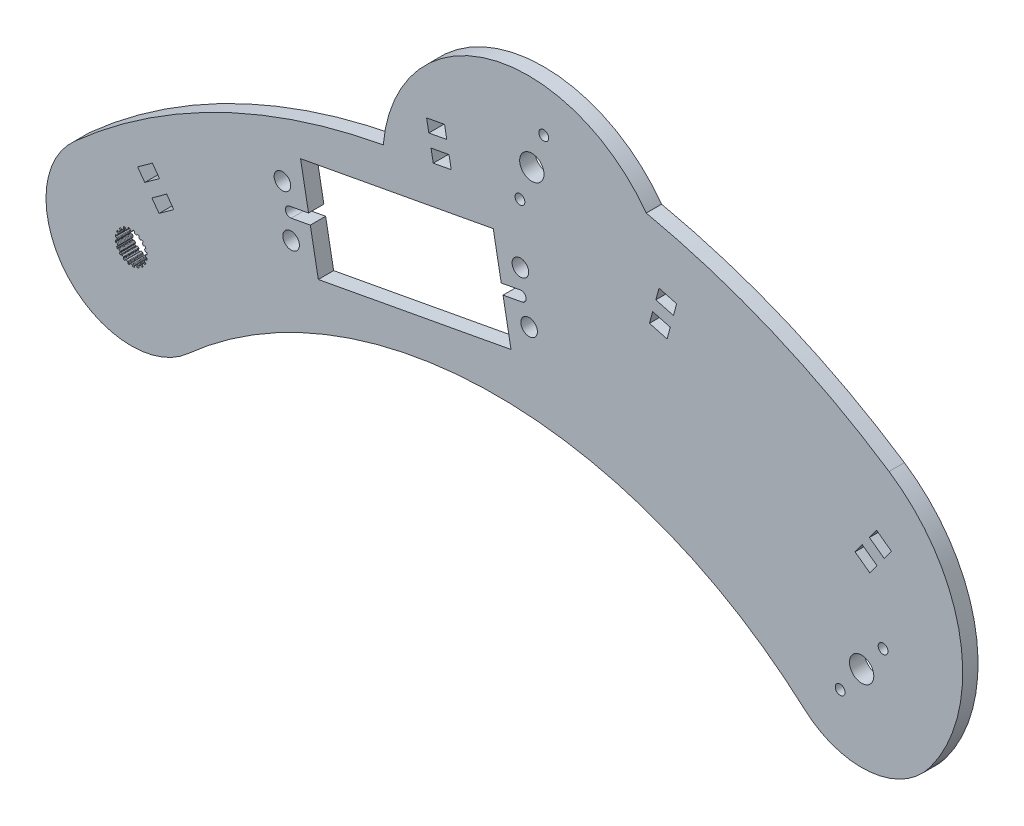
SolidWorks part; units mm, degrees
ref_plane "Front Plane" through (0, 0, 0) normal (0, 0, 1) x (1, 0, 0)
ref_plane "Top Plane" through (0, 0, 0) normal (0, 1, 0) x (1, 0, 0)
ref_plane "Right Plane" through (0, 0, 0) normal (1, 0, 0) x (0, 0, -1)
sketch "Sketch1" plane through (0, 0, 0) normal (0, 0, 1) x (1, 0, 0)
  line L0 (-0.1069, 2.9699) -> (0.1069, 2.9699)
  line L1 (0.3159, 3.2375) -> (0.2537, 3.0575)
  line L2 (-0.2964, 3.2367) -> (-0.2318, 3.0575)
  line L3 (-0.2964, 3.2367) -> (0.3159, 3.2375) construction
  line L4 (0, 3.3252) -> (0, 0) construction
  line L5 (-0.2318, 3.0575) -> (0.2537, 3.0575) construction
  line L6 (-0.4281, 3.3241) -> (0.4281, 3.3263) construction
  line L7 (0.7183, 3.1698) -> (0.7244, 2.9795)
  line L8 (0.816, 2.8576) -> (1.0195, 2.7915)
  line L9 (1.3009, 2.9815) -> (1.1862, 2.8295)
  line L10 (1.6627, 2.7927) -> (1.6097, 2.6099)
  line L11 (1.6591, 2.4655) -> (1.8322, 2.3398)
  line L12 (2.1585, 2.4335) -> (2.0025, 2.3245)
  line L13 (2.4443, 2.1423) -> (2.3374, 1.9847)
  line L14 (2.3398, 1.8322) -> (2.4655, 1.6591)
  line L15 (2.8049, 1.6474) -> (2.6228, 1.5919)
  line L16 (2.9866, 1.2821) -> (2.8363, 1.1653)
  line L17 (2.7915, 1.0195) -> (2.8576, 0.816)
  line L18 (3.1767, 0.7) -> (2.9863, 0.7035)
  line L19 (3.2367, 0.2964) -> (3.0575, 0.2318)
  line L20 (2.9699, 0.1069) -> (2.9699, -0.1069)
  line L21 (3.2375, -0.3159) -> (3.0575, -0.2537)
  line L22 (3.1698, -0.7183) -> (2.9795, -0.7244)
  line L23 (2.8576, -0.816) -> (2.7915, -1.0195)
  line L24 (2.9815, -1.3009) -> (2.8295, -1.1862)
  line L25 (2.7927, -1.6627) -> (2.6099, -1.6097)
  line L26 (2.4655, -1.6591) -> (2.3398, -1.8322)
  line L27 (2.4335, -2.1585) -> (2.3245, -2.0025)
  line L28 (2.1423, -2.4443) -> (1.9847, -2.3374)
  line L29 (1.8322, -2.3398) -> (1.6591, -2.4655)
  line L30 (1.6474, -2.8049) -> (1.5919, -2.6228)
  line L31 (1.2821, -2.9866) -> (1.1653, -2.8363)
  line L32 (1.0195, -2.7915) -> (0.816, -2.8576)
  line L33 (0.7, -3.1767) -> (0.7035, -2.9863)
  line L34 (0.2964, -3.2367) -> (0.2318, -3.0575)
  line L35 (0.1069, -2.9699) -> (-0.1069, -2.9699)
  line L36 (-0.3159, -3.2375) -> (-0.2537, -3.0575)
  line L37 (-0.7183, -3.1698) -> (-0.7244, -2.9795)
  line L38 (-0.816, -2.8576) -> (-1.0195, -2.7915)
  line L39 (-1.3009, -2.9815) -> (-1.1862, -2.8295)
  line L40 (-1.6627, -2.7927) -> (-1.6097, -2.6099)
  line L41 (-1.6591, -2.4655) -> (-1.8322, -2.3398)
  line L42 (-2.1585, -2.4335) -> (-2.0025, -2.3245)
  line L43 (-2.4443, -2.1423) -> (-2.3374, -1.9847)
  line L44 (-2.3398, -1.8322) -> (-2.4655, -1.6591)
  line L45 (-2.8049, -1.6474) -> (-2.6228, -1.5919)
  line L46 (-2.9866, -1.2821) -> (-2.8363, -1.1653)
  line L47 (-2.7915, -1.0195) -> (-2.8576, -0.816)
  line L48 (-3.1767, -0.7) -> (-2.9863, -0.7035)
  line L49 (-3.2367, -0.2964) -> (-3.0575, -0.2318)
  line L50 (-2.9699, -0.1069) -> (-2.9699, 0.1069)
  line L51 (-3.2375, 0.3159) -> (-3.0575, 0.2537)
  line L52 (-3.1698, 0.7183) -> (-2.9795, 0.7244)
  line L53 (-2.8576, 0.816) -> (-2.7915, 1.0195)
  line L54 (-2.9815, 1.3009) -> (-2.8295, 1.1862)
  line L55 (-2.7927, 1.6627) -> (-2.6099, 1.6097)
  line L56 (-2.4655, 1.6591) -> (-2.3398, 1.8322)
  line L57 (-2.4335, 2.1585) -> (-2.3245, 2.0025)
  line L58 (-2.1423, 2.4443) -> (-1.9847, 2.3374)
  line L59 (-1.8322, 2.3398) -> (-1.6591, 2.4655)
  line L60 (-1.6474, 2.8049) -> (-1.5919, 2.6228)
  line L61 (-1.2821, 2.9866) -> (-1.1653, 2.8363)
  line L62 (-1.0195, 2.7915) -> (-0.816, 2.8576)
  line L63 (-0.7, 3.1767) -> (-0.7035, 2.9863)
  line L64 (0.4281, 3.3263) -> (0.62, 3.2938)
  line L65 (1.4351, 3.0312) -> (1.6075, 2.9409)
  line L66 (2.3015, 2.4394) -> (2.4376, 2.3003)
  line L67 (2.9427, 1.6088) -> (3.0291, 1.4344)
  line L68 (3.2958, 0.6207) -> (3.3241, 0.4281)
  line L69 (3.3263, -0.4281) -> (3.2938, -0.62)
  line L70 (3.0312, -1.4351) -> (2.9409, -1.6075)
  line L71 (2.4394, -2.3015) -> (2.3003, -2.4376)
  line L72 (1.6088, -2.9427) -> (1.4344, -3.0291)
  line L73 (0.6207, -3.2958) -> (0.4281, -3.3241)
  line L74 (-0.4281, -3.3263) -> (-0.62, -3.2938)
  line L75 (-1.4351, -3.0312) -> (-1.6075, -2.9409)
  line L76 (-2.3015, -2.4394) -> (-2.4376, -2.3003)
  line L77 (-2.9427, -1.6088) -> (-3.0291, -1.4344)
  line L78 (-3.2958, -0.6207) -> (-3.3241, -0.4281)
  line L79 (-3.3263, 0.4281) -> (-3.2938, 0.62)
  line L80 (-3.0312, 1.4351) -> (-2.9409, 1.6075)
  line L81 (-2.4394, 2.3015) -> (-2.3003, 2.4376)
  line L82 (-1.6088, 2.9427) -> (-1.4344, 3.0291)
  line L83 (-0.6207, 3.2958) -> (-0.4281, 3.3241)
  line L84 (-11.8753, 13.2369) -> (11.8753, -13.2369) construction
  line L85 (164.2753, 13.2369) -> (140.5247, -13.2369) construction
  line L86 (0, 0) -> (152.4, 0) construction
  arc A0 (0.2537, 3.0575) -> (0.1069, 2.9699) centre (0.1283, 3.1009) cw
  arc A1 (-0.2318, 3.0575) -> (-0.1069, 2.9699) centre (-0.1069, 3.1026) ccw
  arc A2 (0.62, 3.2938) -> (0.7183, 3.1698) centre (0.5856, 3.1656) cw
  arc A3 (0.7244, 2.9795) -> (0.816, 2.8576) centre (0.857, 2.9838) ccw
  arc A4 (-0.4281, 3.3241) -> (-0.2964, 3.2367) centre (-0.4213, 3.1916) cw
  arc A5 (0.4281, 3.3263) -> (0.3159, 3.2375) centre (0.4413, 3.1942) ccw
  arc A6 (1.1862, 2.8295) -> (1.0195, 2.7915) centre (1.0802, 2.9095) cw
  arc A7 (1.4351, 3.0312) -> (1.3009, 2.9815) centre (1.4068, 2.9015) ccw
  arc A8 (1.6075, 2.9409) -> (1.6627, 2.7927) centre (1.5352, 2.8297) cw
  arc A9 (1.6097, 2.6099) -> (1.6591, 2.4655) centre (1.7371, 2.5729) ccw
  arc A10 (2.0025, 2.3245) -> (1.8322, 2.3398) centre (1.9264, 2.4332) cw
  arc A11 (2.3015, 2.4394) -> (2.1585, 2.4335) centre (2.2346, 2.3248) ccw
  arc A12 (2.4376, 2.3003) -> (2.4443, 2.1423) centre (2.3345, 2.2168) cw
  arc A13 (2.3374, 1.9847) -> (2.3398, 1.8322) centre (2.4472, 1.9102) ccw
  arc A14 (2.6228, 1.5919) -> (2.4655, 1.6591) centre (2.5841, 1.7189) cw
  arc A15 (2.9427, 1.6088) -> (2.8049, 1.6474) centre (2.8436, 1.5205) ccw
  arc A16 (3.0291, 1.4344) -> (2.9866, 1.2821) centre (2.9052, 1.3869) cw
  arc A17 (2.8363, 1.1653) -> (2.7915, 1.0195) centre (2.9177, 1.0605) ccw
  arc A18 (2.9863, 0.7035) -> (2.8576, 0.816) centre (2.9887, 0.8362) cw
  arc A19 (3.2958, 0.6207) -> (3.1767, 0.7) centre (3.1743, 0.5673) ccw
  arc A20 (3.3241, 0.4281) -> (3.2367, 0.2964) centre (3.1916, 0.4213) cw
  arc A21 (3.0575, 0.2318) -> (2.9699, 0.1069) centre (3.1026, 0.1069) ccw
  arc A22 (3.0575, -0.2537) -> (2.9699, -0.1069) centre (3.1009, -0.1283) cw
  arc A23 (3.3263, -0.4281) -> (3.2375, -0.3159) centre (3.1942, -0.4413) ccw
  arc A24 (3.2938, -0.62) -> (3.1698, -0.7183) centre (3.1656, -0.5856) cw
  arc A25 (2.9795, -0.7244) -> (2.8576, -0.816) centre (2.9838, -0.857) ccw
  arc A26 (2.8295, -1.1862) -> (2.7915, -1.0195) centre (2.9095, -1.0802) cw
  arc A27 (3.0312, -1.4351) -> (2.9815, -1.3009) centre (2.9015, -1.4068) ccw
  arc A28 (2.9409, -1.6075) -> (2.7927, -1.6627) centre (2.8297, -1.5352) cw
  arc A29 (2.6099, -1.6097) -> (2.4655, -1.6591) centre (2.5729, -1.7371) ccw
  arc A30 (2.3245, -2.0025) -> (2.3398, -1.8322) centre (2.4332, -1.9264) cw
  arc A31 (2.4394, -2.3015) -> (2.4335, -2.1585) centre (2.3248, -2.2346) ccw
  arc A32 (2.3003, -2.4376) -> (2.1423, -2.4443) centre (2.2168, -2.3345) cw
  arc A33 (1.9847, -2.3374) -> (1.8322, -2.3398) centre (1.9102, -2.4472) ccw
  arc A34 (1.5919, -2.6228) -> (1.6591, -2.4655) centre (1.7189, -2.5841) cw
  arc A35 (1.6088, -2.9427) -> (1.6474, -2.8049) centre (1.5205, -2.8436) ccw
  arc A36 (1.4344, -3.0291) -> (1.2821, -2.9866) centre (1.3869, -2.9052) cw
  arc A37 (1.1653, -2.8363) -> (1.0195, -2.7915) centre (1.0605, -2.9177) ccw
  arc A38 (0.7035, -2.9863) -> (0.816, -2.8576) centre (0.8362, -2.9887) cw
  arc A39 (0.6207, -3.2958) -> (0.7, -3.1767) centre (0.5673, -3.1743) ccw
  arc A40 (0.4281, -3.3241) -> (0.2964, -3.2367) centre (0.4213, -3.1916) cw
  arc A41 (0.2318, -3.0575) -> (0.1069, -2.9699) centre (0.1069, -3.1026) ccw
  arc A42 (-0.2537, -3.0575) -> (-0.1069, -2.9699) centre (-0.1283, -3.1009) cw
  arc A43 (-0.4281, -3.3263) -> (-0.3159, -3.2375) centre (-0.4413, -3.1942) ccw
  arc A44 (-0.62, -3.2938) -> (-0.7183, -3.1698) centre (-0.5856, -3.1656) cw
  arc A45 (-0.7244, -2.9795) -> (-0.816, -2.8576) centre (-0.857, -2.9838) ccw
  arc A46 (-1.1862, -2.8295) -> (-1.0195, -2.7915) centre (-1.0802, -2.9095) cw
  arc A47 (-1.4351, -3.0312) -> (-1.3009, -2.9815) centre (-1.4068, -2.9015) ccw
  arc A48 (-1.6075, -2.9409) -> (-1.6627, -2.7927) centre (-1.5352, -2.8297) cw
  arc A49 (-1.6097, -2.6099) -> (-1.6591, -2.4655) centre (-1.7371, -2.5729) ccw
  arc A50 (-2.0025, -2.3245) -> (-1.8322, -2.3398) centre (-1.9264, -2.4332) cw
  arc A51 (-2.3015, -2.4394) -> (-2.1585, -2.4335) centre (-2.2346, -2.3248) ccw
  arc A52 (-2.4376, -2.3003) -> (-2.4443, -2.1423) centre (-2.3345, -2.2168) cw
  arc A53 (-2.3374, -1.9847) -> (-2.3398, -1.8322) centre (-2.4472, -1.9102) ccw
  arc A54 (-2.6228, -1.5919) -> (-2.4655, -1.6591) centre (-2.5841, -1.7189) cw
  arc A55 (-2.9427, -1.6088) -> (-2.8049, -1.6474) centre (-2.8436, -1.5205) ccw
  arc A56 (-3.0291, -1.4344) -> (-2.9866, -1.2821) centre (-2.9052, -1.3869) cw
  arc A57 (-2.8363, -1.1653) -> (-2.7915, -1.0195) centre (-2.9177, -1.0605) ccw
  arc A58 (-2.9863, -0.7035) -> (-2.8576, -0.816) centre (-2.9887, -0.8362) cw
  arc A59 (-3.2958, -0.6207) -> (-3.1767, -0.7) centre (-3.1743, -0.5673) ccw
  arc A60 (-3.3241, -0.4281) -> (-3.2367, -0.2964) centre (-3.1916, -0.4213) cw
  arc A61 (-3.0575, -0.2318) -> (-2.9699, -0.1069) centre (-3.1026, -0.1069) ccw
  arc A62 (-3.0575, 0.2537) -> (-2.9699, 0.1069) centre (-3.1009, 0.1283) cw
  arc A63 (-3.3263, 0.4281) -> (-3.2375, 0.3159) centre (-3.1942, 0.4413) ccw
  arc A64 (-3.2938, 0.62) -> (-3.1698, 0.7183) centre (-3.1656, 0.5856) cw
  arc A65 (-2.9795, 0.7244) -> (-2.8576, 0.816) centre (-2.9838, 0.857) ccw
  arc A66 (-2.8295, 1.1862) -> (-2.7915, 1.0195) centre (-2.9095, 1.0802) cw
  arc A67 (-3.0312, 1.4351) -> (-2.9815, 1.3009) centre (-2.9015, 1.4068) ccw
  arc A68 (-2.9409, 1.6075) -> (-2.7927, 1.6627) centre (-2.8297, 1.5352) cw
  arc A69 (-2.6099, 1.6097) -> (-2.4655, 1.6591) centre (-2.5729, 1.7371) ccw
  arc A70 (-2.3245, 2.0025) -> (-2.3398, 1.8322) centre (-2.4332, 1.9264) cw
  arc A71 (-2.4394, 2.3015) -> (-2.4335, 2.1585) centre (-2.3248, 2.2346) ccw
  arc A72 (-2.3003, 2.4376) -> (-2.1423, 2.4443) centre (-2.2168, 2.3345) cw
  arc A73 (-1.9847, 2.3374) -> (-1.8322, 2.3398) centre (-1.9102, 2.4472) ccw
  arc A74 (-1.5919, 2.6228) -> (-1.6591, 2.4655) centre (-1.7189, 2.5841) cw
  arc A75 (-1.6088, 2.9427) -> (-1.6474, 2.8049) centre (-1.5205, 2.8436) ccw
  arc A76 (-1.4344, 3.0291) -> (-1.2821, 2.9866) centre (-1.3869, 2.9052) cw
  arc A77 (-1.1653, 2.8363) -> (-1.0195, 2.7915) centre (-1.0605, 2.9177) ccw
  arc A78 (-0.7035, 2.9863) -> (-0.816, 2.8576) centre (-0.8362, 2.9887) cw
  arc A79 (-0.6207, 3.2958) -> (-0.7, 3.1767) centre (-0.5673, 3.1743) ccw
  circle A80 centre (0, 0) radius 12.7 construction
  arc A81 (-11.8753, 13.2369) -> (164.2753, 13.2369) centre (76.2, -84.9368) cw
  arc A82 (11.8753, -13.2369) -> (140.5247, -13.2369) centre (76.2, -84.9368) cw
  arc A84 (-11.8753, 13.2369) -> (11.8753, -13.2369) centre (0, 0) ccw
  arc A85 (164.2753, 13.2369) -> (140.5247, -13.2369) centre (152.4, 0) cw
  point P14 (0, 2.9699)
  point P26 (0, 0)
  point P247 (0, 0)
  dimension "D4" = 0.1327
  dimension "D8" = 20
  dimension "D9" = 25.4
  dimension "D10" = 131.8914
  dimension "D1" = 2.9699
  dimension "D2" = 0.2139
  dimension "D3" = 0.1904
  dimension "D5" = 0.0877
  dimension "D6" = 0.4855
  dimension "D7" = 0.8563
  dimension "D11" = 35.5662
  dimension "D12" = 152.4
extrude "Boss-Extrude1" add sketch "Sketch1" along normal blind 3.2004
sketch "Sketch4" plane through (0, 0, 3.2004) normal (0, 0, 1) x (1, 0, 0)
  line L1 (83.5881, 56.2861) -> (152.4, 0) construction
  line L2 (83.5881, 56.2861) -> (83.1655, 46.7705) construction
  arc A0 (52.583, 44.8229) -> (113.2282, 41.6501) centre (82.8478, 42.1322) cw
  arc A1 (140.5247, -13.2369) -> (164.2753, 13.2369) centre (152.4, 0) ccw construction
  arc A3 (164.2753, 13.2369) -> (-11.8753, 13.2369) centre (76.2, -84.9368) ccw construction
  circle A4 centre (83.5881, 56.2861) radius 2.54
  arc A10 (113.2282, 41.6501) -> (52.583, 44.8229) centre (76.2, -84.9368) ccw
  dimension "D4" = 5.08
  dimension "D5" = 57.1766
  dimension "D3" = 30.3842
  dimension "D1" = 9.525
  dimension "D2" = 88.9
  dimension "D6" = 60.7281
  dimension "D7" = 53.261
extrude "Boss-Extrude3" add sketch "Sketch4" against normal up to surface (3.2004 mm away) up to face at (76.2, 8.6481, 0)
sketch "Sketch2" plane through (0, 0, 3.2004) normal (0, 0, 1) x (1, 0, 0)
  line L7 (164.2753, 13.2369) -> (140.5247, -13.2369) construction
  line L19 (81.2013, 36.9705) -> (83.0244, 27.1381) construction
  line L20 (31.5476, 27.764) -> (33.3707, 17.9316) construction
  line L24 (82.1128, 32.0543) -> (32.4591, 22.8478) construction
  line L31 (35.3294, 33.7132) -> (75.5381, 41.1684)
  line L32 (35.3294, 33.7132) -> (39.0339, 13.7337)
  line L33 (39.0339, 13.7337) -> (79.2426, 21.189)
  line L34 (75.5381, 41.1684) -> (79.2426, 21.189)
  line L35 (55.4338, 37.4408) -> (59.1382, 17.4613) construction
  circle A7 centre (83.0244, 27.1381) radius 1.7272
  circle A9 centre (31.5476, 27.764) radius 1.7272
  circle A10 centre (33.3707, 17.9316) radius 1.7272
  circle A11 centre (81.2013, 36.9705) radius 1.7272
  circle A13 centre (66.9709, 29.2468) radius 3.429 construction
  arc A14 (0, 0) -> (152.4, 0) centre (76.2, -84.9368) cw construction
  arc A15 (-11.8753, 13.2369) -> (11.8753, -13.2369) centre (0, 0) ccw construction
  arc A16 (140.5247, -13.2369) -> (164.2753, 13.2369) centre (152.4, 0) ccw construction
  arc A17 (164.2753, 13.2369) -> (113.2282, 41.6501) centre (76.2, -84.9368) ccw construction
  circle A18 centre (152.4, 0) radius 2.54
  circle A19 centre (83.5881, 56.2861) radius 2.54 construction
  circle A20 centre (83.5881, 56.2861) radius 2.54 construction
  point P0 (66.9709, 29.2468)
  point P30 (32.8713, 20.6251)
  point P40 (57.286, 27.4511)
  dimension "D2" = 15.4
  dimension "D3" = 6.858
  dimension "D5" = 3.4544
  dimension "D6" = 2.2606
  dimension "D7" = 31.7373
  dimension "D1" = 50.5
  dimension "D4" = 10
  dimension "D12" = 20.32
  dimension "D13" = 40.894
extrude "Cut-Extrude1" cut sketch "Sketch2" against normal up to surface (3.2004 mm away) up to face at (78.5906, 20.6529, 0)
sketch "Sketch5" plane through (0, 0, 0) normal (0, 0, -1) x (-1, 0, 0)
  line L0 (-86.0718, 63.3017) -> (-81.1043, 49.2706) construction
  line L1 (0, 0) -> (-152.4, 0) construction
  circle A0 centre (-86.0718, 63.3017) radius 1.025
  circle A1 centre (-81.1043, 49.2706) radius 1.025
  circle A4 centre (-83.5881, 56.2861) radius 2.54 construction
  point P10 (-83.5881, 56.2861)
  dimension "D1" = 2.05
  dimension "D2" = 70.504
  dimension "D3" = 14.8844
sketch "Sketch6" plane through (0, 0, 3.2004) normal (0, 0, 1) x (1, 0, 0)
  line L0 (156.8788, 5.9436) -> (147.9212, -5.9436) construction
  line L1 (0, 0) -> (152.4, 0) construction
  circle A0 centre (147.9212, -5.9436) radius 1.025
  circle A1 centre (156.8788, 5.9436) radius 1.025
  dimension "D1" = 2.05
  dimension "D2" = 127
  dimension "D3" = 14.8844
extrude "Cut-Extrude2" cut sketch "Sketch5" against normal up to surface (3.2004 mm away) up to face at (154.94, 0, 3.2004)
extrude "Cut-Extrude3" cut sketch "Sketch6" against normal up to surface (3.2004 mm away) up to face at (85.0468, 63.3017, 0)
sketch "Sketch7" plane through (0, 0, 0) normal (0, 0, 1) x (1, 0, 0)
  line L0 (158.1231, 38.5869) -> (166.6312, -10.6636) construction
  arc A0 (107.4588, 59.9507) -> (158.1231, 38.5869) centre (76.2, -84.9368) cw
  arc A1 (158.1231, 38.5869) -> (83.89, 63.0847) centre (76.2, -84.9368) ccw construction
  arc A4 (113.2282, 41.6501) -> (52.583, 44.8229) centre (82.8478, 42.1322) ccw construction
  arc A5 (158.1231, 38.5869) -> (166.6312, -10.6636) centre (139.1275, 9.9453) cw
  arc A6 (166.6312, -10.6636) -> (158.1231, 38.5869) centre (139.1275, 9.9453) ccw construction
  arc A7 (164.2753, 13.2369) -> (166.6312, -10.6636) centre (152.4, 0) cw
  arc A8 (140.5247, -13.2369) -> (164.2753, 13.2369) centre (152.4, 0) ccw construction
  arc A9 (113.2282, 41.6501) -> (164.2753, 13.2369) centre (76.2, -84.9368) cw
  arc A10 (164.2753, 13.2369) -> (113.2282, 41.6501) centre (76.2, -84.9368) ccw construction
  arc A11 (107.4588, 59.9507) -> (113.2282, 41.6501) centre (82.8478, 42.1322) cw
  arc A12 (113.2282, 41.6501) -> (52.583, 44.8229) centre (82.8478, 42.1322) ccw construction
extrude "Boss-Extrude4" add sketch "Sketch7" along normal up to surface (3.2004 mm away) up to face at (148.9462, -5.9436, 3.2004)
sketch "Sketch8" plane through (0, 0, 0) normal (0, 0, -1) x (-1, 0, 0)
  line L0 (-111.6319, 45.9923) -> (-110.3049, 41.0887) construction
  line L5 (-3.6206, 15.312) -> (-6.5996, 11.1972) construction
  line L6 (4.7519, 5.2968) -> (0, 0) construction
  line L7 (11.953, -1.1635) -> (-2.4491, 11.7571) construction
  line L8 (-156.3207, 24.5097) -> (-153.3199, 20.4107) construction
  line L9 (-109.1295, 44.0381) -> (-112.8073, 43.0429) construction
  line L10 (-156.3574, 21.3349) -> (-153.2832, 23.5854) construction
  line L11 (-113.4708, 45.4947) -> (-109.7931, 46.4899) construction
  line L12 (-113.8025, 46.7206) -> (-110.1248, 47.7159)
  line L13 (-113.8025, 46.7206) -> (-113.139, 44.2688)
  line L14 (-113.139, 44.2688) -> (-109.4613, 45.264)
  line L15 (-110.1248, 47.7159) -> (-109.4613, 45.264)
  line L20 (-112.1438, 40.5911) -> (-108.466, 41.5863) construction
  line L21 (-112.4755, 41.817) -> (-108.7978, 42.8122)
  line L22 (-112.4755, 41.817) -> (-111.812, 39.3652)
  line L23 (-111.812, 39.3652) -> (-108.1343, 40.3604)
  line L24 (-108.7978, 42.8122) -> (-108.1343, 40.3604)
  line L25 (-157.8578, 23.3844) -> (-154.7835, 25.635) construction
  line L26 (-158.608, 24.4092) -> (-155.5337, 26.6597)
  line L27 (-158.608, 24.4092) -> (-157.1076, 22.3597)
  line L28 (-157.1076, 22.3597) -> (-154.0333, 24.6102)
  line L29 (-155.5337, 26.6597) -> (-154.0333, 24.6102)
  line L30 (-154.8571, 19.2854) -> (-151.7828, 21.5359) construction
  line L31 (-155.6073, 20.3101) -> (-152.533, 22.5607)
  line L32 (-155.6073, 20.3101) -> (-154.1069, 18.2606)
  line L33 (-154.1069, 18.2606) -> (-151.0326, 20.5112)
  line L34 (-152.533, 22.5607) -> (-151.0326, 20.5112)
  line L35 (-163.8646, 15.214) -> (-152.4, 0) construction
  line L36 (-6.6532, 14.3717) -> (-3.5671, 12.1374) construction
  line L37 (-2.0775, 14.1948) -> (-5.1636, 16.4291) construction
  line L38 (-2.8223, 13.1661) -> (-5.9084, 15.4004)
  line L39 (-2.8223, 13.1661) -> (-1.3328, 15.2235)
  line L40 (-1.3328, 15.2235) -> (-4.4188, 17.4578)
  line L41 (-5.9084, 15.4004) -> (-4.4188, 17.4578)
  line L42 (-5.0566, 10.08) -> (-8.1427, 12.3143) construction
  line L43 (-5.8014, 9.0513) -> (-8.8875, 11.2856)
  line L44 (-5.8014, 9.0513) -> (-4.3118, 11.1087)
  line L45 (-4.3118, 11.1087) -> (-7.3979, 13.343)
  line L46 (-8.8875, 11.2856) -> (-7.3979, 13.343)
  line L47 (-63.7364, 53.3338) -> (-64.6626, 48.3389) construction
  line L48 (-66.0726, 51.1836) -> (-62.3264, 50.489) construction
  line L49 (-61.8634, 52.9865) -> (-65.6095, 53.681) construction
  line L50 (-62.0949, 51.7377) -> (-65.841, 52.4323)
  line L51 (-62.0949, 51.7377) -> (-61.6318, 54.2352)
  line L52 (-61.6318, 54.2352) -> (-65.378, 54.9298)
  line L53 (-65.841, 52.4323) -> (-65.378, 54.9298)
  line L54 (-62.7895, 47.9916) -> (-66.5356, 48.6862) construction
  line L55 (-63.021, 46.7429) -> (-66.7672, 47.4375)
  line L56 (-63.021, 46.7429) -> (-62.558, 49.2403)
  line L57 (-62.558, 49.2403) -> (-66.3041, 49.9349)
  line L58 (-66.7672, 47.4375) -> (-66.3041, 49.9349)
  line L59 (-75.5381, 41.1684) -> (-35.3294, 33.7132) construction
  arc A0 (-11.8753, -13.2369) -> (11.8753, 13.2369) centre (0, 0) ccw construction
  arc A1 (-163.8646, 15.214) -> (-110.0014, 43.7983) centre (-76.2, -84.9368) cw construction
  circle A6 centre (-152.4, 0) radius 2.54 construction
  circle A7 centre (-156.8788, 5.9436) radius 1.025 construction
  arc A8 (-107.4588, 59.9507) -> (-158.1231, 38.5869) centre (-76.2, -84.9368) ccw construction
  arc A9 (-31.5476, 27.764) -> (4.7519, 5.2968) centre (-76.2, -84.9368) cw construction
  arc A10 (11.8753, 13.2369) -> (-52.583, 44.8229) centre (-76.2, -84.9368) ccw construction
  circle A11 centre (-31.5476, 27.764) radius 1.7272 construction
  point P11 (-156.8788, 5.9436)
  point P19 (-5.1101, 13.2546)
  point P26 (-154.8203, 22.4602)
  point P27 (-110.9684, 43.5405)
  point P76 (-64.1995, 50.8363)
  dimension "D3" = 19.05
  dimension "D4" = 3.81
  dimension "D5" = 2.54
  dimension "D6" = 3.81
  dimension "D7" = 5.08
extrude "Cut-Extrude4" cut sketch "Sketch8" against normal up to surface (3.2004 mm away) up to face at (148.9462, -5.9436, 3.2004)
sketch "Sketch9" plane through (0, 0, 0) normal (0, 0, -1) x (-1, 0, 0)
  line L2 (-79.2426, 21.189) -> (-75.5381, 41.1684) construction
  line L3 (-35.3294, 33.7132) -> (-39.0339, 13.7337) construction
  line L4 (-81.201, 32.9186) -> (-77.2051, 32.1777)
  line L5 (-81.201, 32.9186) -> (-81.5715, 30.9206) construction
  line L7 (-81.5715, 30.9206) -> (-77.5756, 30.1797)
  line L8 (-77.2051, 32.1777) -> (-77.5756, 30.1797)
  line L9 (-36.9964, 24.7224) -> (-33.0005, 23.9815)
  line L10 (-36.9964, 24.7224) -> (-37.3669, 22.7245)
  line L11 (-37.3669, 22.7245) -> (-33.371, 21.9836)
  line L12 (-33.0005, 23.9815) -> (-33.371, 21.9836) construction
  arc A6 (-33.0005, 23.9815) -> (-33.371, 21.9836) centre (-33.1858, 22.9826) cw
  arc A7 (-81.201, 32.9186) -> (-81.5715, 30.9206) centre (-81.3862, 31.9196) ccw
  point P22 (-77.3903, 31.1787)
  point P23 (-37.1816, 23.7235)
  dimension "D4" = 4.064
  dimension "D5" = 2.032
extrude "Cut-Extrude5" cut sketch "Sketch9" against normal up to surface (3.2004 mm away) up to face at (6.5996, 11.1972, 3.2004)
